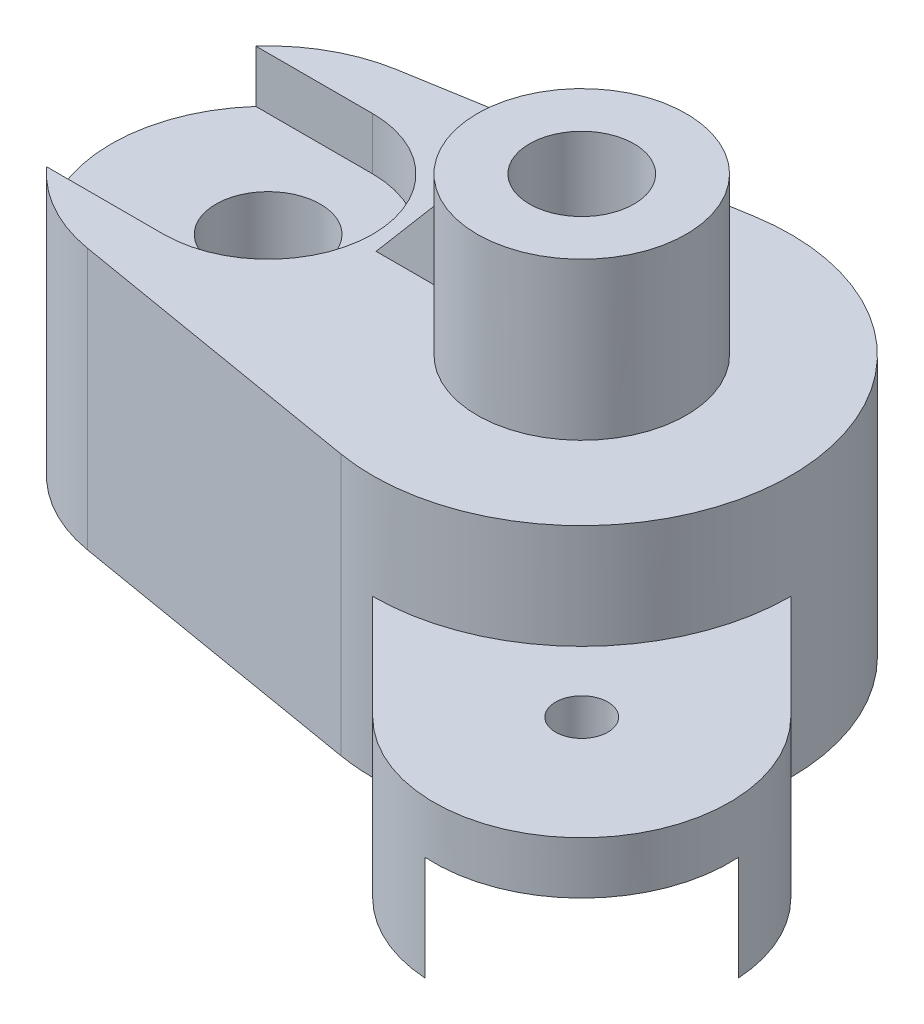
SolidWorks part; units mm, degrees
ref_plane "Front Plane" through (0, 0, 0) normal (0, 0, 1) x (1, 0, 0)
ref_plane "Top Plane" through (0, 0, 0) normal (0, 1, 0) x (1, 0, 0)
ref_plane "Right Plane" through (0, 0, 0) normal (1, 0, 0) x (0, 0, -1)
sketch "Sketch1" plane through (0, 0, 0) normal (0, 1, 0) x (1, 0, 0)
  line L0 (0, 59.2486) -> (0, -62.6796) construction
  line L1 (-6.6667, 39.4405) -> (-65, 29.5804)
  line L2 (-65, -29.5804) -> (-6.6667, -39.4405)
  arc A0 (0, -40) -> (0, 40) centre (0, 0) ccw
  arc A1 (-82.3607, 20) -> (-82.3607, -20) centre (-60, 0) ccw
  arc A2 (-82.3607, 20) -> (-65, 29.5804) centre (-60, 0) cw
  arc A3 (0, 40) -> (-6.6667, 39.4405) centre (0, 0) ccw
  arc A4 (-82.3607, -20) -> (-65, -29.5804) centre (-60, 0) ccw
  arc A5 (0, -40) -> (-6.6667, -39.4405) centre (0, 0) cw
  dimension "D1" = 80
  dimension "D3" = 30
  dimension "D2" = 60
  dimension "D4" = 20
  dimension "D5" = 20
  dimension "D6" = 20
extrude "Boss-Extrude1" add sketch "Sketch1" along normal blind 50
sketch "Sketch2" plane through (0, 0, 0) normal (0, -1, 0) x (1, 0, 0)
  circle A0 centre (0, 0) radius 30
  dimension "D1" = 60
extrude "Cut-Extrude1" cut sketch "Sketch2" against normal blind 30
sketch "Sketch3" plane through (0, 50, 0) normal (0, 1, 0) x (1, 0, 0)
  circle A0 centre (0, 0) radius 20
  dimension "D1" = 40
extrude "Boss-Extrude2" add sketch "Sketch3" along normal blind 30
sketch "Sketch4" plane through (0, 80, 0) normal (0, 1, 0) x (1, 0, 0)
  point P0 (0, 0)
hole_wizard "Ø20.0mm Dowel Hole1" positions "3DSketch1" profile "Sketch5" hole size "Ø20.0" standard "ISO"
sketch3d "3DSketch1"
  point P0 (0, 80, 0)
sketch "Sketch5" plane through (0, 80, 0) normal (1, 0, 0) x (0, 0, 1)
  line L0 (0, 0) -> (0, 36.0086)
  line L1 (0, 36.0086) -> (10, 30)
  line L2 (10, 30) -> (10, 0)
  line L5 (10, 0) -> (0, 0)
  line L10 (0, 36.0086) -> (-10, 30) construction
  line L11 (0, -6.35) -> (0, 107.95) construction
  dimension "Hole Dia." = 20
  dimension "Hole Depth" = 30
  dimension "Drill Angle" = 118
sketch "Sketch6" plane through (0, 50, 0) normal (0, 1, 0) x (1, 0, 0)
  circle A0 centre (-60, 0) radius 10
  dimension "D1" = 20
extrude "Cut-Extrude2" cut sketch "Sketch6" against normal blind 109
sketch "Sketch7" plane through (0, 50, 0) normal (0, 1, 0) x (1, 0, 0)
  line L0 (-60, 20) -> (-82.3607, 20)
  line L1 (-60, -20) -> (-82.3607, -20)
  arc A0 (-60, 20) -> (-60, -20) centre (-60, 0) cw
  arc A1 (-65, 29.5804) -> (-65, -29.5804) centre (-60, 0) ccw construction
  arc A2 (-82.3607, 20) -> (-82.3607, -20) centre (-60, 0) ccw
  circle M1 centre (-60, 0) radius 10
  arc M4 (-65, 29.5804) -> (-65, -29.5804) centre (-60, 0) ccw
  dimension "D1" = 20
  dimension "D2" = 20
  dimension "D3" = 40
  dimension "D4" = 22.3607
extrude "Cut-Extrude3" cut sketch "Sketch7" against normal blind 10 contours A0 L0 L1 M4 M1
ref_plane "Plane1" through (-6.6667, 50, 39.4405) normal (0, -1, 0) x (-1, 0, 0)
sketch "Sketch10" plane through (0, 0, 0) normal (0, -1, 0) x (1, 0, 0)
  line L0 (0, 40) -> (20, 60)
  line L1 (40, 0) -> (60, 20)
  line L2 (0, 0) -> (97.3698, 97.3698) construction
  line L3 (0, 0) -> (-141.3283, 0) construction
  line L6 (-65, -29.5804) -> (-6.6667, -39.4405)
  line L7 (-6.6667, 39.4405) -> (-65, 29.5804)
  line L8 (-65, -29.5804) -> (-6.6667, -39.4405)
  line L9 (-6.6667, 39.4405) -> (-65, 29.5804)
  arc A0 (-6.6667, -39.4405) -> (40, 0) centre (0, 0) ccw
  arc A1 (-6.6667, -39.4405) -> (-6.6667, 39.4405) centre (0, 0) ccw construction
  arc A2 (60, 20) -> (20, 60) centre (40, 40) ccw
  arc A3 (40, 0) -> (0, 40) centre (0, 0) ccw
  arc A4 (-6.6667, -39.4405) -> (-6.6667, 39.4405) centre (0, 0) ccw
  arc A5 (-65, 29.5804) -> (-65, -29.5804) centre (-60, 0) ccw
  arc A6 (0, 40) -> (-6.6667, 39.4405) centre (0, 0) ccw
  arc A7 (-65, 29.5804) -> (-65, -29.5804) centre (-60, 0) ccw
  arc M8 (-6.6667, -39.4405) -> (-6.6667, 39.4405) centre (0, 0) ccw
  dimension "D1" = 0
  dimension "D2" = 40
  dimension "D3" = 40
  dimension "D4" = 135
  dimension "D5" = 40
  dimension "D7" = 40
  dimension "D6" = 0
extrude "Boss-Extrude3" add sketch "Sketch10" against normal blind 30 contours L1 A2 L0 M8
sketch "Sketch11" plane through (0, 0, 0) normal (0, -1, 0) x (-1, 0, 0)
  line L0 (0, 0) -> (150.5849, 0) construction
  line L1 (0, 0) -> (-106.7459, -106.7459) construction
  circle A0 centre (-40, -40) radius 5
  dimension "D3" = 10
  dimension "D1" = 150.5849
  dimension "D2" = 135
extrude "Cut-Extrude4" cut sketch "Sketch11" against normal blind 30
ref_plane "Plane2" through (-6.6667, 50, 39.4405) normal (0.986, 0, 0.1667) x (0.1667, 0, -0.986)
sketch "Sketch13" plane through (0, 0, 0) normal (0, -1, 0) x (-1, 0, 0)
  line L0 (-38.2288, -68.2288) -> (0, -30)
  line L1 (-68.2288, -38.2288) -> (-30, 0)
  line L2 (0, 0) -> (119.6248, 0) construction
  line L3 (0, 0) -> (-102.2571, -102.2571) construction
  line L4 (-68.2288, -38.2288) -> (-30, 0)
  arc A0 (-60, -20) -> (-20, -60) centre (-40, -40) ccw construction
  arc A2 (-68.2288, -38.2288) -> (-38.2288, -68.2288) centre (-40, -40) ccw
  arc A3 (-30, 0) -> (0, -30) centre (0, 0) ccw
  circle M1 centre (-40, -40) radius 5
  circle M3 centre (0, 0) radius 30
  arc M7 (-60, -20) -> (-20, -60) centre (-40, -40) ccw
  dimension "D1" = 135
  dimension "D2" = 30
  dimension "D3" = 30
  dimension "D4" = 0
extrude "Cut-Extrude5" cut sketch "Sketch13" against normal blind 20 contours L1 L0 M7 M3 M1
sketch "Sketch14" plane through (0, 50, 0) normal (0, 1, 0) x (1, 0, 0)
  line L1 (-19.8431, 2.5) -> (-36.8431, 2.5)
  line L2 (-19.8431, 2.5) -> (-19.8431, -2.5)
  line L3 (-19.8431, -2.5) -> (-36.8431, -2.5)
  line L4 (-36.8431, 2.5) -> (-36.8431, -2.5)
  circle A0 centre (0, 0) radius 20 construction
  dimension "D1" = 5
  dimension "D2" = 2.5
  dimension "D3" = 17
extrude "Boss-Extrude4" add sketch "Sketch14" along normal blind 20
sketch "Sketch15" plane through (0, 0, 0) normal (0, -1, 0) x (1, 0, 0)
  line L1 (-105.6113, -20) -> (-14.3887, -20)
  line L2 (-105.6113, -20) -> (-105.6113, 20)
  line L3 (-105.6113, 20) -> (-14.3887, 20)
  line L4 (-14.3887, -20) -> (-14.3887, 20)
  line L5 (-105.6113, -20) -> (-14.3887, 20) construction
  line L6 (-105.6113, 20) -> (-14.3887, -20) construction
  point P0 (-60, 0)
  dimension "D1" = 40
extrude "Cut-Extrude6" cut sketch "Sketch15" against normal blind 20
sketch "Sketch16" plane through (0, 0, 2.5) normal (0, 0, 1) x (1, 0, 0)
  line L0 (-19.8431, 70) -> (-36.8431, 50)
  line L1 (-36.8431, 50) -> (-36.8431, 70)
  line L2 (-36.8431, 70) -> (-19.8431, 70)
extrude "Cut-Extrude7" cut sketch "Sketch16" against normal blind 20
